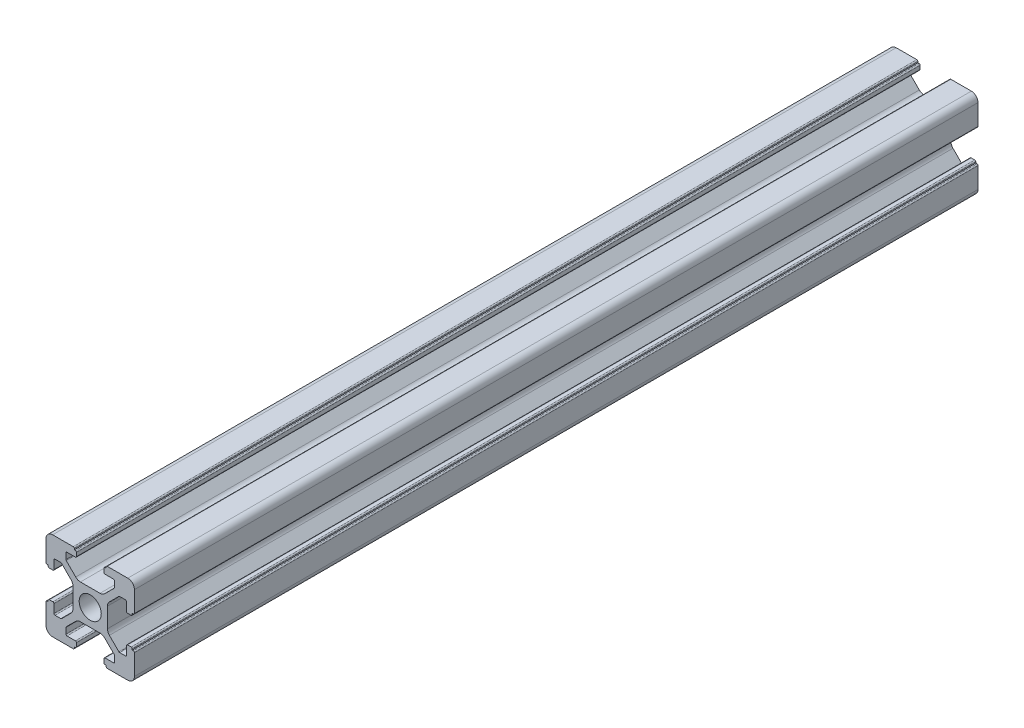
SolidWorks part; units mm, degrees
material "1060 Alloy"
ref_plane "前视基准面" through (0, 0, 0) normal (0, 0, 1) x (1, 0, 0)
ref_plane "上视基准面" through (0, 0, 0) normal (0, 1, 0) x (1, 0, 0)
ref_plane "右视基准面" through (0, 0, 0) normal (1, 0, 0) x (0, 0, -1)
sketch "草图1" plane through (0, 0, 0) normal (0, 0, 1) x (1, 0, 0)
  line L0 (0, 0) -> (0, 5.5) construction
  line L1 (-8.5023, -10.0023) -> (-3.85, -10.0023)
  line L2 (-10.0023, -8.5023) -> (-10.0023, -3.85)
  line L3 (-8.5023, 10.0023) -> (-3.85, 10.0023)
  line L4 (10.0023, -8.5023) -> (10.0023, -3.85)
  line L5 (-10.0023, -10.0023) -> (10.0023, 10.0023) construction
  line L6 (-10.0023, 10.0023) -> (10.0023, -10.0023) construction
  line L7 (-2.218, -3.9) -> (2.218, -3.9)
  line L8 (-3.9, -2.218) -> (-3.9, 2.218)
  line L9 (-2.218, 3.9) -> (2.218, 3.9)
  line L10 (3.9, -2.218) -> (3.9, 2.218)
  line L11 (-3.9, -3.9) -> (3.9, 3.9) construction
  line L12 (-3.9, 3.9) -> (3.9, -3.9) construction
  line L13 (-5.25, -8.2) -> (-3.35, -8.2)
  line L14 (-8.2, -5.25) -> (-8.2, -3.35)
  line L15 (-5.25, 8.2) -> (-3.35, 8.2)
  line L16 (8.2, -5.25) -> (8.2, -3.35)
  line L17 (-8.2, -8.2) -> (8.2, 8.2) construction
  line L18 (-8.2, 8.2) -> (8.2, -8.2) construction
  line L19 (-7.95, 5.5) -> (-6.6642, 5.5)
  line L20 (0, 0) -> (5.5, 0) construction
  line L23 (-5.5, 7.95) -> (-5.5, 6.6642)
  line L26 (0, 0) -> (-0.5303, 0.5303)
  line L27 (3.2787, 4.3393) -> (5.4268, 6.4874)
  line L28 (0, 0) -> (0.5303, -0.5303)
  line L29 (5.5, 6.6642) -> (5.5, 7.95)
  line L30 (4.3393, 3.2787) -> (6.4874, 5.4268)
  line L31 (6.6642, 5.5) -> (7.95, 5.5)
  line L32 (4.3393, -3.2787) -> (6.4874, -5.4268)
  line L33 (3.2787, -4.3393) -> (5.4268, -6.4874)
  line L34 (-3.2787, -4.3393) -> (-5.4268, -6.4874)
  line L35 (-4.3393, -3.2787) -> (-6.4874, -5.4268)
  line L36 (-4.3393, 3.2787) -> (-6.4874, 5.4268)
  line L37 (-3.2787, 4.3393) -> (-5.4268, 6.4874)
  line L38 (3.1, -8.45) -> (3.1, -9.2523)
  line L39 (8.45, 3.1) -> (9.2523, 3.1)
  line L40 (-5.5, -6.6642) -> (-5.5, -7.95)
  line L41 (-6.6642, -5.5) -> (-7.95, -5.5)
  line L42 (5.5, -6.6642) -> (5.5, -7.95)
  line L43 (6.6642, -5.5) -> (7.95, -5.5)
  line L44 (9.2523, -3.1) -> (8.45, -3.1)
  line L46 (10.0023, 3.85) -> (10.0023, 8.5023)
  line L47 (8.2, 3.35) -> (8.2, 5.25)
  line L48 (-3.1, -9.2523) -> (-3.1, -8.45)
  line L49 (-8.45, -3.1) -> (-9.2523, -3.1)
  line L50 (-9.2523, 3.1) -> (-8.45, 3.1)
  line L51 (-3.1, 8.45) -> (-3.1, 9.2523)
  line L52 (3.1, 9.2523) -> (3.1, 8.45)
  line L53 (3.85, 10.0023) -> (8.5023, 10.0023)
  line L54 (3.35, 8.2) -> (5.25, 8.2)
  line L55 (-10.0023, 3.85) -> (-10.0023, 8.5023)
  line L56 (-8.2, 3.35) -> (-8.2, 5.25)
  line L57 (3.35, -8.2) -> (5.25, -8.2)
  line L58 (3.85, -10.0023) -> (8.5023, -10.0023)
  line L59 (9.7523, -3.6) -> (9.5023, -3.6)
  line L61 (9.7523, 3.6) -> (9.5023, 3.6)
  line L62 (9.5023, -3.6) -> (9.5023, -3.35)
  line L63 (3.6, -9.7523) -> (3.6, -9.5023)
  line L64 (3.35, -9.5023) -> (3.6, -9.5023)
  line L65 (9.5023, 3.35) -> (9.5023, 3.6)
  line L66 (-3.6, -9.5023) -> (-3.35, -9.5023)
  line L67 (-3.6, -9.7523) -> (-3.6, -9.5023)
  line L68 (-9.7523, -3.6) -> (-9.5023, -3.6)
  line L69 (-9.5023, -3.35) -> (-9.5023, -3.6)
  line L70 (-9.5023, 3.6) -> (-9.5023, 3.35)
  line L71 (-9.7523, 3.6) -> (-9.5023, 3.6)
  line L72 (-3.6, 9.7523) -> (-3.6, 9.5023)
  line L73 (-3.35, 9.5023) -> (-3.6, 9.5023)
  line L74 (3.6, 9.5023) -> (3.35, 9.5023)
  line L75 (3.6, 9.7523) -> (3.6, 9.5023)
  circle A0 centre (0, 0) radius 2.5
  arc A1 (10.0023, 8.5023) -> (8.5023, 10.0023) centre (8.5023, 8.5023) ccw
  arc A2 (8.5023, -10.0023) -> (10.0023, -8.5023) centre (8.5023, -8.5023) ccw
  arc A3 (-10.0023, -8.5023) -> (-8.5023, -10.0023) centre (-8.5023, -8.5023) ccw
  arc A4 (-10.0023, 8.5023) -> (-8.5023, 10.0023) centre (-8.5023, 8.5023) cw
  arc A5 (-9.5023, -3.35) -> (-9.2523, -3.1) centre (-9.2523, -3.35) cw
  arc A6 (-9.7523, -3.6) -> (-10.0023, -3.85) centre (-9.7523, -3.85) ccw
  arc A7 (-8.45, -3.1) -> (-8.2, -3.35) centre (-8.45, -3.35) cw
  arc A8 (-7.95, -5.5) -> (-8.2, -5.25) centre (-7.95, -5.25) cw
  arc A9 (-6.4874, -5.4268) -> (-6.6642, -5.5) centre (-6.6642, -5.25) cw
  arc A10 (-5.4268, -6.4874) -> (-5.5, -6.6642) centre (-5.25, -6.6642) ccw
  arc A11 (-5.5, -7.95) -> (-5.25, -8.2) centre (-5.25, -7.95) ccw
  arc A12 (-3.6, -9.7523) -> (-3.85, -10.0023) centre (-3.85, -9.7523) cw
  arc A13 (-3.35, -9.5023) -> (-3.1, -9.2523) centre (-3.35, -9.2523) ccw
  arc A14 (-3.1, -8.45) -> (-3.35, -8.2) centre (-3.35, -8.45) ccw
  arc A15 (3.1, -8.45) -> (3.35, -8.2) centre (3.35, -8.45) cw
  arc A16 (5.5, -7.95) -> (5.25, -8.2) centre (5.25, -7.95) cw
  arc A17 (5.4268, -6.4874) -> (5.5, -6.6642) centre (5.25, -6.6642) cw
  arc A18 (6.4874, -5.4268) -> (6.6642, -5.5) centre (6.6642, -5.25) ccw
  arc A19 (7.95, -5.5) -> (8.2, -5.25) centre (7.95, -5.25) ccw
  arc A20 (8.45, -3.1) -> (8.2, -3.35) centre (8.45, -3.35) ccw
  arc A21 (9.5023, -3.35) -> (9.2523, -3.1) centre (9.2523, -3.35) ccw
  arc A22 (9.7523, -3.6) -> (10.0023, -3.85) centre (9.7523, -3.85) cw
  arc A23 (3.35, -9.5023) -> (3.1, -9.2523) centre (3.35, -9.2523) cw
  arc A24 (3.6, -9.7523) -> (3.85, -10.0023) centre (3.85, -9.7523) ccw
  arc A25 (7.95, 5.5) -> (8.2, 5.25) centre (7.95, 5.25) cw
  arc A26 (8.2, 3.35) -> (8.45, 3.1) centre (8.45, 3.35) ccw
  arc A27 (9.5023, 3.35) -> (9.2523, 3.1) centre (9.2523, 3.35) cw
  arc A28 (9.7523, 3.6) -> (10.0023, 3.85) centre (9.7523, 3.85) ccw
  arc A29 (6.6642, 5.5) -> (6.4874, 5.4268) centre (6.6642, 5.25) ccw
  arc A30 (5.4268, 6.4874) -> (5.5, 6.6642) centre (5.25, 6.6642) ccw
  arc A31 (5.5, 7.95) -> (5.25, 8.2) centre (5.25, 7.95) ccw
  arc A32 (3.1, 8.45) -> (3.35, 8.2) centre (3.35, 8.45) ccw
  arc A33 (3.6, 9.7523) -> (3.85, 10.0023) centre (3.85, 9.7523) cw
  arc A34 (3.35, 9.5023) -> (3.1, 9.2523) centre (3.35, 9.2523) ccw
  arc A35 (-9.7523, 3.6) -> (-10.0023, 3.85) centre (-9.7523, 3.85) cw
  arc A36 (-9.5023, 3.35) -> (-9.2523, 3.1) centre (-9.2523, 3.35) ccw
  arc A37 (-8.45, 3.1) -> (-8.2, 3.35) centre (-8.45, 3.35) ccw
  arc A38 (-8.2, 5.25) -> (-7.95, 5.5) centre (-7.95, 5.25) cw
  arc A39 (-6.4874, 5.4268) -> (-6.6642, 5.5) centre (-6.6642, 5.25) ccw
  arc A40 (-5.4268, 6.4874) -> (-5.5, 6.6642) centre (-5.25, 6.6642) cw
  arc A41 (-5.5, 7.95) -> (-5.25, 8.2) centre (-5.25, 7.95) cw
  arc A42 (-3.1, 8.45) -> (-3.35, 8.2) centre (-3.35, 8.45) cw
  arc A43 (-3.1, 9.2523) -> (-3.35, 9.5023) centre (-3.35, 9.2523) ccw
  arc A44 (-3.6, 9.7523) -> (-3.85, 10.0023) centre (-3.85, 9.7523) ccw
  arc A45 (-4.3393, 3.2787) -> (-3.9, 2.218) centre (-5.4, 2.218) cw
  arc A46 (-3.2787, 4.3393) -> (-2.218, 3.9) centre (-2.218, 5.4) ccw
  arc A47 (3.2787, 4.3393) -> (2.218, 3.9) centre (2.218, 5.4) cw
  arc A48 (4.3393, 3.2787) -> (3.9, 2.218) centre (5.4, 2.218) ccw
  arc A49 (4.3393, -3.2787) -> (3.9, -2.218) centre (5.4, -2.218) cw
  arc A50 (3.2787, -4.3393) -> (2.218, -3.9) centre (2.218, -5.4) ccw
  arc A51 (-4.3393, -3.2787) -> (-3.9, -2.218) centre (-5.4, -2.218) ccw
  arc A52 (-2.218, -3.9) -> (-3.2787, -4.3393) centre (-2.218, -5.4) ccw
  point P0 (0, 0)
  point P7 (10.0023, 0)
  point P62 (0, 0)
  point P76 (0, 0)
  point P92 (-8.2, -5.5)
  point P99 (0, 0)
  point P106 (-5.5, -8.2)
  point P117 (5.5, -8.2)
  point P124 (8.2, -5.5)
  point P137 (8.2, 5.5)
  point P140 (8.2, 3.1)
  point P147 (6.5607, 5.5)
  point P152 (5.5, 8.2)
  point P167 (-8.2, 5.5)
  point P174 (-5.5, 8.2)
  dimension "D1" = 1.5
  dimension "D5" = 0.25
  dimension "D6" = 1.5
  dimension "D2" = 4
  dimension "D3" = 4
  dimension "D4" = 4
extrude "凸台-拉伸1" add sketch "草图1" along normal blind 190.86 contours A52 L7 A50 L33 A17 L42 A16 L57 A15 L38 A23 L64 L63 A24 L58 A2 L4 A22 L59 L62 A21 L44 A20 L16 A19 L43 A18 L32 A49 L10 A48 L30 A29 L31 A25 L47 A26 L39 A27 L65 L61 A28 L46 A1 L53 A33 L75 L74 A34 L52 A32
ref_plane "Plane1" through (0, 0, 95.43) normal (0, 0, 1) x (1, 0, 0)
